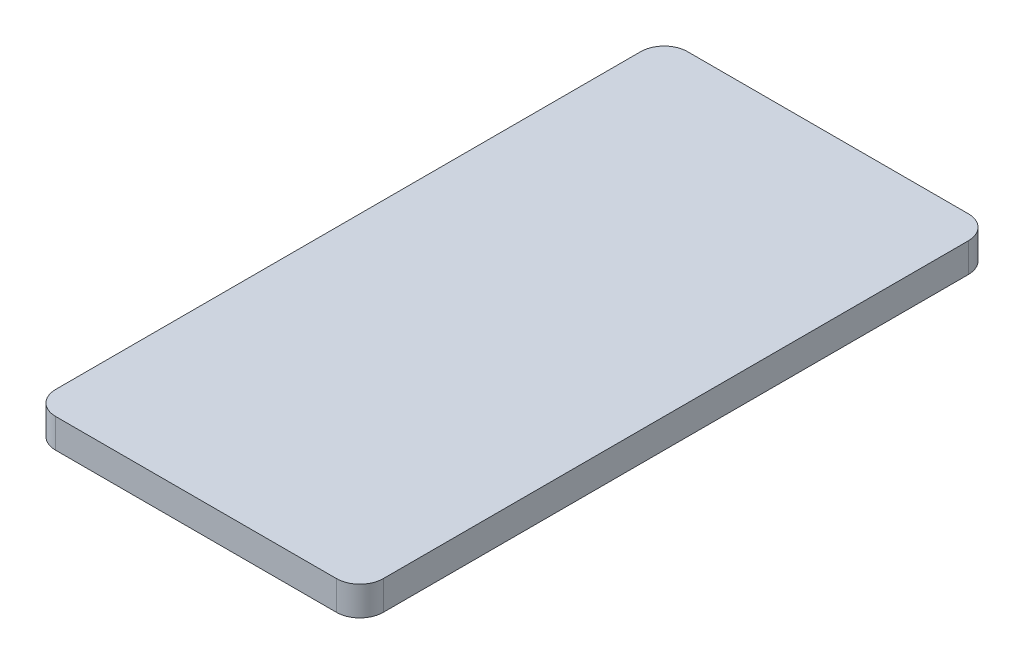
SolidWorks part; units mm, degrees
ref_plane "Front Plane" through (0, 0, 0) normal (0, 0, 1) x (1, 0, 0)
ref_plane "Top Plane" through (0, 0, 0) normal (0, 1, 0) x (1, 0, 0)
ref_plane "Right Plane" through (0, 0, 0) normal (1, 0, 0) x (0, 0, -1)
sketch "Sketch1" plane through (0, 0, 0) normal (0, 1, 0) x (1, 0, 0)
  line L1 (-15.24, -34.29) -> (15.24, -34.29)
  line L2 (-17.78, -31.75) -> (-17.78, 31.75)
  line L3 (-15.24, 34.29) -> (15.24, 34.29)
  line L4 (17.78, -31.75) -> (17.78, 31.75)
  line L5 (-17.78, -34.29) -> (17.78, 34.29) construction
  line L6 (-17.78, 34.29) -> (17.78, -34.29) construction
  arc A0 (15.24, -34.29) -> (17.78, -31.75) centre (15.24, -31.75) ccw
  arc A1 (-15.24, -34.29) -> (-17.78, -31.75) centre (-15.24, -31.75) cw
  arc A2 (15.24, 34.29) -> (17.78, 31.75) centre (15.24, 31.75) cw
  arc A3 (-17.78, 31.75) -> (-15.24, 34.29) centre (-15.24, 31.75) cw
  point P0 (0, 0)
  dimension "D3" = 2.54
  dimension "D1" = 35.56
  dimension "D2" = 68.58
extrude "Boss-Extrude1" add sketch "Sketch1" along normal blind 3.175
